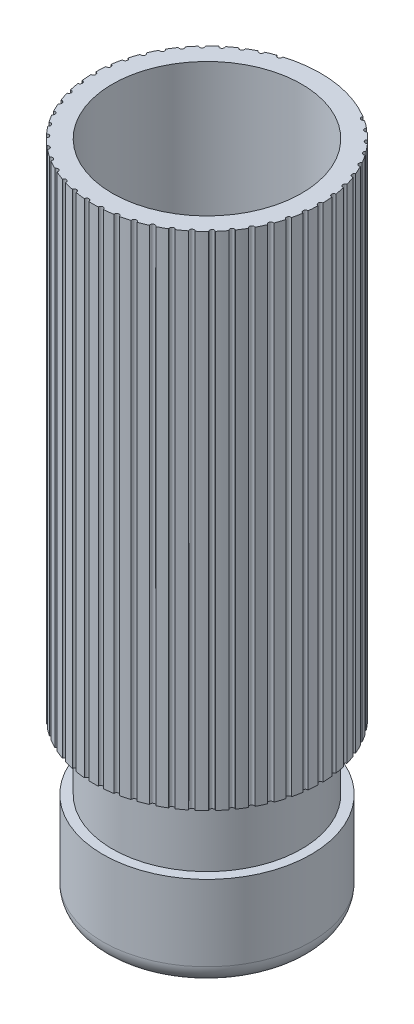
SolidWorks part; units mm, degrees
ref_plane "前视基准面" through (0, 0, 0) normal (0, 0, 1) x (1, 0, 0)
ref_plane "上视基准面" through (0, 0, 0) normal (0, 1, 0) x (1, 0, 0)
ref_plane "右视基准面" through (0, 0, 0) normal (1, 0, 0) x (0, 0, -1)
sketch "草图1" plane through (0, 0, 0) normal (0, 1, 0) x (1, 0, 0)
  circle A0 centre (0, 0) radius 12
  dimension "D1" = 24
extrude "凸台-拉伸1" add sketch "草图1" along normal blind 50
shell "抽壳3" thickness 2
sketch "草图2" plane through (0, 0, 0) normal (0, -1, 0) x (1, 0, 0)
  circle A0 centre (0, 0) radius 12
extrude "凸台-拉伸2" add sketch "草图2" along normal blind 20
sketch "草图3" plane through (0, 0, 0) normal (0, 0, 1) x (1, 0, 0)
  line L0 (0, -0.5356) -> (0, -25.133) construction
  line L1 (0, -25.133) -> (0, 9.9198) construction
  line L2 (16.9514, -20) -> (-17.9805, -20) construction
  line L3 (11, -10) -> (11, -20)
  line L4 (11, -10) -> (10, -10)
  line L5 (10, -10) -> (10, -3)
  line L6 (10, -3) -> (12.743, -3)
  line L7 (12.743, -3) -> (12.743, -20)
  line L8 (12.743, -20) -> (11, -20)
  line L9 (12, -20) -> (12, 50) construction
  line L10 (-12, -20) -> (12, -20) construction
  dimension "D1" = 1
  dimension "D2" = 10
  dimension "D3" = 1
  dimension "D4" = 7
revolve "切除-旋转1" cut sketch "草图3" angle 360 about L0
fillet "圆角1" radius 2 1 edges at (-11, -20, 0)
sketch "草图5" plane through (0, 50, 0) normal (0, 1, 0) x (1, 0, 0)
  line L0 (-13.2, 0) -> (13.2, 0) construction
  circle A0 centre (12, 0) radius 0.25
  circle A2 centre (0, 0) radius 12 construction
extrude "切除-拉伸1" cut sketch "草图5" against normal blind 54
sketch "草图7" plane through (0, 0, 0) normal (0, 0, 1) x (1, 0, 0)
  line L0 (0, 59.9374) -> (0, -34.3656) construction
pattern_circular "阵列(圆周)1" count 50 over 360 about axis through (0, 0, 0) along (0, 1, 0) skipping 36, 37, 38, 39, 40, 41 of "切除-拉伸1"
sketch "草图10" plane through (0, 50, 0) normal (0, 1, 0) x (1, 0, 0)
  circle A0 centre (0, 0) radius 10
curve "螺旋线/涡状线1" pitch 0.5 height 8 turns 16
